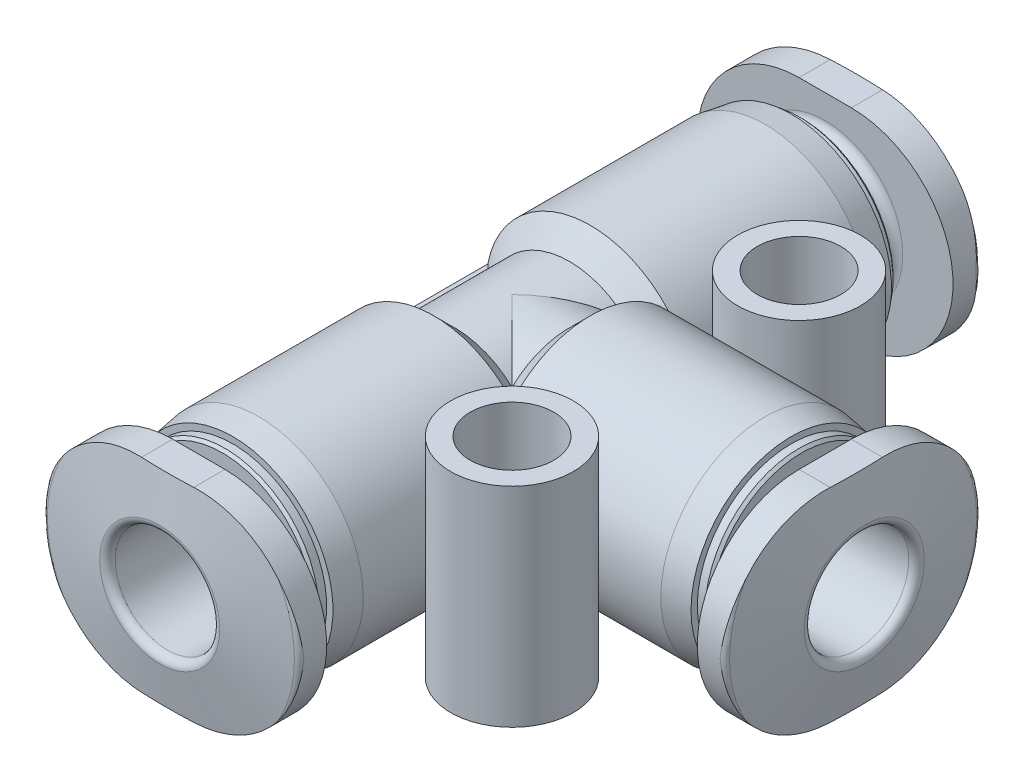
SolidWorks part; units mm, degrees
ref_plane "Front Plane" through (0, 0, 0) normal (0, 0, 1) x (1, 0, 0)
ref_plane "Top Plane" through (0, 0, 0) normal (0, 1, 0) x (1, 0, 0)
ref_plane "Right Plane" through (0, 0, 0) normal (1, 0, 0) x (0, 0, -1)
ref_plane "Plane1" through (0, 0, 0) normal (1, 0, 0) x (0, 0, -1)
sketch "Sketch1" plane through (0, 0, 0) normal (1, 0, 0) x (0, 0, -1)
  line L0 (-13.5, 0) -> (-13.5, 2.3)
  line L1 (-13.5, 2.3) -> (-13.0707, 4.7347)
  line L2 (-12.8737, 4.9) -> (-12, 4.9)
  line L3 (-12, 4.9) -> (-12, 2.975)
  line L4 (-11.625, 2.6) -> (-11.1, 2.6)
  line L5 (-11.1, 2.6) -> (-11.1, 3.5)
  line L6 (-11.1, 3.5) -> (-11, 3.6)
  line L7 (-11, 3.6) -> (-10.7, 3.6)
  line L8 (-10.7, 3.6) -> (-10.7, 3.8416)
  line L9 (-10.7, 3.8416) -> (-9.7, 4)
  line L10 (-9.7, 4) -> (-3, 4)
  line L11 (-3, 4) -> (-2.2, 3.2)
  line L12 (-2.2, 3.2) -> (2.2, 3.2)
  line L13 (2.2, 3.2) -> (3, 4)
  line L14 (3, 4) -> (9.7, 4)
  line L15 (9.7, 4) -> (10.7, 3.8416)
  line L16 (10.7, 3.8416) -> (10.7, 3.6)
  line L17 (10.7, 3.6) -> (11, 3.6)
  line L18 (11, 3.6) -> (11.1, 3.5)
  line L19 (11.1, 3.5) -> (11.1, 2.6)
  line L20 (11.1, 2.6) -> (11.625, 2.6)
  line L21 (12, 2.975) -> (12, 4.9)
  line L22 (12, 4.9) -> (12.8737, 4.9)
  line L23 (13.0707, 4.7347) -> (13.5, 2.3)
  line L24 (13.5, 2.3) -> (13.5, 0)
  line L25 (13.5, 0) -> (-13.5, 0)
  line L26 (13.5, 0) -> (-13.5, 0) construction
  arc A0 (-13.0707, 4.7347) -> (-12.8737, 4.9) centre (-12.8737, 4.7) cw
  arc A1 (-12, 2.975) -> (-11.625, 2.6) centre (-11.625, 2.975) ccw
  arc A2 (11.625, 2.6) -> (12, 2.975) centre (11.625, 2.975) ccw
  arc A3 (12.8737, 4.9) -> (13.0707, 4.7347) centre (12.8737, 4.7) cw
revolve "Revolve1" add sketch "Sketch1" angle 360 about L26
ref_plane "Plane2" through (0, 0, -13.5) normal (0, 0, 1) x (1, 0, 0)
sketch "Sketch2" plane through (0, 0, -13.5) normal (0, 0, 1) x (1, 0, 0)
  line L0 (-20, -20) -> (20, -20)
  line L1 (20, -20) -> (20, 20)
  line L2 (20, 20) -> (-20, 20)
  line L3 (-20, 20) -> (-20, -20)
  line L4 (-1, -3.9) -> (1, -3.9)
  line L5 (1, 3.9) -> (-1, 3.9)
  arc A0 (-1, 3.9) -> (-1, -3.9) centre (-1, 0) ccw
  arc A1 (1, -3.9) -> (1, 3.9) centre (1, 0) ccw
extrude "Cut-Extrude1" cut sketch "Sketch2" along normal blind 1.5
ref_plane "Plane3" through (0, 0, 13.5) normal (0, 0, 1) x (1, 0, 0)
sketch "Sketch3" plane through (0, 0, 13.5) normal (0, 0, 1) x (1, 0, 0)
  line L0 (-20, -20) -> (20, -20)
  line L1 (20, -20) -> (20, 20)
  line L2 (20, 20) -> (-20, 20)
  line L3 (-20, 20) -> (-20, -20)
  line L4 (-1, -3.9) -> (1, -3.9)
  line L5 (1, 3.9) -> (-1, 3.9)
  arc A0 (-1, 3.9) -> (-1, -3.9) centre (-1, 0) ccw
  arc A1 (1, -3.9) -> (1, 3.9) centre (1, 0) ccw
extrude "Cut-Extrude2" cut sketch "Sketch3" against normal blind 1.5
ref_plane "Plane4" through (0, 0, 0) normal (0, 1, 0) x (1, 0, 0)
sketch "Sketch4" plane through (0, 0, 0) normal (0, 1, 0) x (1, 0, 0)
  line L0 (0, 0) -> (0, 3.2)
  line L1 (0, 3.2) -> (2.2, 3.2)
  line L2 (2.2, 3.2) -> (3, 4)
  line L3 (3, 4) -> (9.7, 4)
  line L4 (9.7, 4) -> (10.7, 3.8416)
  line L5 (10.7, 3.8416) -> (10.7, 3.6)
  line L6 (10.7, 3.6) -> (11, 3.6)
  line L7 (11, 3.6) -> (11.1, 3.5)
  line L8 (11.1, 3.5) -> (11.1, 2.6)
  line L9 (11.1, 2.6) -> (11.625, 2.6)
  line L10 (12, 2.975) -> (12, 4.9)
  line L11 (12, 4.9) -> (12.8737, 4.9)
  line L12 (13.0707, 4.7347) -> (13.5, 2.3)
  line L13 (13.5, 2.3) -> (13.5, 0)
  line L14 (13.5, 0) -> (0, 0)
  line L15 (13.5, 0) -> (0, 0) construction
  arc A0 (11.625, 2.6) -> (12, 2.975) centre (11.625, 2.975) ccw
  arc A1 (12.8737, 4.9) -> (13.0707, 4.7347) centre (12.8737, 4.7) cw
revolve "Revolve2" add sketch "Sketch4" angle 360 about L15
ref_plane "Plane5" through (13.5, 0, 0) normal (1, 0, 0) x (0, 0, -1)
sketch "Sketch5" plane through (13.5, 0, 0) normal (1, 0, 0) x (0, 0, -1)
  line L0 (-20, -20) -> (20, -20)
  line L1 (20, -20) -> (20, 20)
  line L2 (20, 20) -> (-20, 20)
  line L3 (-20, 20) -> (-20, -20)
  line L4 (-1, -3.9) -> (1, -3.9)
  line L5 (1, 3.9) -> (-1, 3.9)
  arc A0 (-1, 3.9) -> (-1, -3.9) centre (-1, 0) ccw
  arc A1 (1, -3.9) -> (1, 3.9) centre (1, 0) ccw
extrude "Cut-Extrude3" cut sketch "Sketch5" against normal blind 1.5
ref_plane "Plane6" through (0, 0, 0) normal (0, 0, 1) x (1, 0, 0)
sketch "Sketch6" plane through (0, 0, 0) normal (0, 0, 1) x (1, 0, 0)
  line L0 (-3.9291, -0.75) -> (0, -0.75)
  line L1 (0, -0.75) -> (0, 0.75)
  line L2 (0, 0.75) -> (-3.9291, 0.75)
  arc A0 (-3.9291, 0.75) -> (-3.9291, -0.75) centre (0, 0) ccw
extrude "Boss-Extrude1" add sketch "Sketch6" against normal blind 3 and the other way blind 3
ref_plane "Plane7" through (5.5, 0, 0) normal (1, 0, 0) x (0, 0, -1)
sketch "Sketch7" plane through (5.5, 0, 0) normal (1, 0, 0) x (0, 0, -1)
  line L0 (-5.5, -4) -> (-7.85, -4)
  line L1 (-7.85, -4) -> (-7.85, 4)
  line L2 (-7.85, 4) -> (-5.5, 4)
  line L3 (-5.5, 4) -> (-5.5, -4)
  line L4 (-5.5, 4) -> (-5.5, -4) construction
revolve "Revolve3" add sketch "Sketch7" angle 360 about L4
ref_plane "Plane8" through (5.5, 0, 0) normal (1, 0, 0) x (0, 0, -1)
sketch "Sketch8" plane through (5.5, 0, 0) normal (1, 0, 0) x (0, 0, -1)
  line L0 (5.5, -4) -> (3.15, -4)
  line L1 (3.15, -4) -> (3.15, 4)
  line L2 (3.15, 4) -> (5.5, 4)
  line L3 (5.5, 4) -> (5.5, -4)
  line L4 (5.5, 4) -> (5.5, -4) construction
revolve "Revolve4" add sketch "Sketch8" angle 360 about L4
ref_plane "Plane9" through (5.5, 0, 0) normal (1, 0, 0) x (0, 0, -1)
sketch "Sketch9" plane through (5.5, 0, 0) normal (1, 0, 0) x (0, 0, -1)
  line L0 (-5.5, -4) -> (-7.1, -4)
  line L1 (-7.1, -4) -> (-7.1, 4)
  line L2 (-7.1, 4) -> (-5.5, 4)
  line L3 (-5.5, 4) -> (-5.5, -4)
  line L4 (-5.5, 4) -> (-5.5, -4) construction
revolve "Cut-Revolve1" cut sketch "Sketch9" angle 360 about L4
ref_plane "Plane10" through (5.5, 0, 0) normal (1, 0, 0) x (0, 0, -1)
sketch "Sketch10" plane through (5.5, 0, 0) normal (1, 0, 0) x (0, 0, -1)
  line L0 (5.5, -4) -> (3.9, -4)
  line L1 (3.9, -4) -> (3.9, 4)
  line L2 (3.9, 4) -> (5.5, 4)
  line L3 (5.5, 4) -> (5.5, -4)
  line L4 (5.5, 4) -> (5.5, -4) construction
revolve "Cut-Revolve2" cut sketch "Sketch10" angle 360 about L4
ref_plane "Plane11" through (0, 0, 0) normal (1, 0, 0) x (0, 0, -1)
sketch "Sketch11" plane through (0, 0, 0) normal (1, 0, 0) x (0, 0, -1)
  line L0 (-13.5, 0) -> (-13.5, 2.3)
  line L1 (-13.2, 2) -> (-2.1, 2)
  line L2 (-2, 1.9) -> (-2, 1.5)
  line L3 (-2, 1.5) -> (2, 1.5)
  line L4 (2, 1.5) -> (2, 1.9)
  line L5 (2.1, 2) -> (13.2, 2)
  line L6 (13.5, 2.3) -> (13.5, 0)
  line L7 (13.5, 0) -> (-13.5, 0)
  line L8 (13.5, 0) -> (-13.5, 0) construction
  arc A0 (-13.5, 2.3) -> (-13.2, 2) centre (-13.2, 2.3) ccw
  arc A1 (-2.1, 2) -> (-2, 1.9) centre (-2.1, 1.9) cw
  arc A2 (2, 1.9) -> (2.1, 2) centre (2.1, 1.9) cw
  arc A3 (13.2, 2) -> (13.5, 2.3) centre (13.2, 2.3) ccw
revolve "Cut-Revolve3" cut sketch "Sketch11" angle 360 about L8
ref_plane "Plane12" through (0, 0, 0) normal (0, 1, 0) x (1, 0, 0)
sketch "Sketch12" plane through (0, 0, 0) normal (0, 1, 0) x (1, 0, 0)
  line L0 (0, 0) -> (0, 1.5)
  line L1 (0, 1.5) -> (2, 1.5)
  line L2 (2, 1.5) -> (2, 1.9)
  line L3 (2.1, 2) -> (13.2, 2)
  line L4 (13.5, 2.3) -> (13.5, 0)
  line L5 (13.5, 0) -> (0, 0)
  line L6 (13.5, 0) -> (0, 0) construction
  arc A0 (2, 1.9) -> (2.1, 2) centre (2.1, 1.9) cw
  arc A1 (13.2, 2) -> (13.5, 2.3) centre (13.2, 2.3) ccw
revolve "Cut-Revolve4" cut sketch "Sketch12" angle 360 about L6
